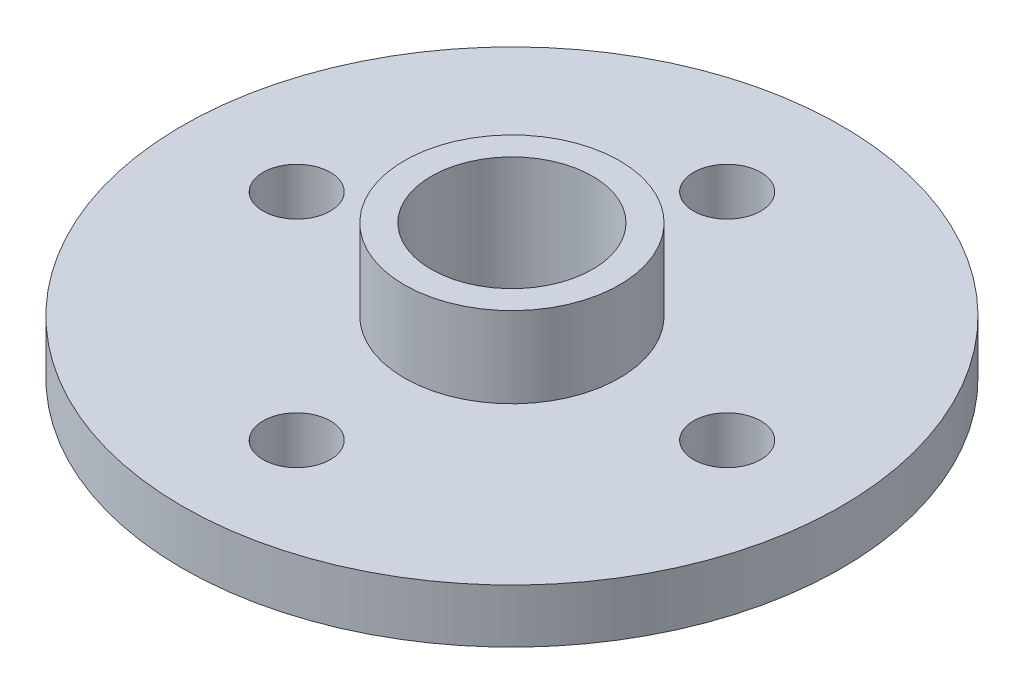
SolidWorks part; units mm, degrees
material "3.0205 (EN-AW 1200)"
ref_plane "Front" through (0, 0, 0) normal (0, 0, 1) x (1, 0, 0)
ref_plane "Top" through (0, 0, 0) normal (0, 1, 0) x (1, 0, 0)
ref_plane "Right" through (0, 0, 0) normal (1, 0, 0) x (0, 0, -1)
sketch "草图1" plane through (0, 0, 0) normal (0, 1, 0) x (1, 0, 0)
  line L0 (0, 0) -> (8, 0) construction
  circle A0 centre (0, 0) radius 12.25
  circle A1 centre (0, 0) radius 3
  circle A2 centre (8, 0) radius 1.25
  circle A3 centre (0, -8) radius 1.25
  circle A4 centre (-8, 0) radius 1.25
  circle A5 centre (0, 8) radius 1.25
  point P15 (0, 0)
  dimension "D1" = 4
extrude "凸台-拉伸1" add sketch "草图1" along normal blind 2
sketch "草图2" plane through (0, 2, 0) normal (0, 1, 0) x (1, 0, 0)
  circle A0 centre (0, 0) radius 3
  circle A1 centre (0, 0) radius 4
extrude "凸台-拉伸2" add sketch "草图2" along normal blind 3
